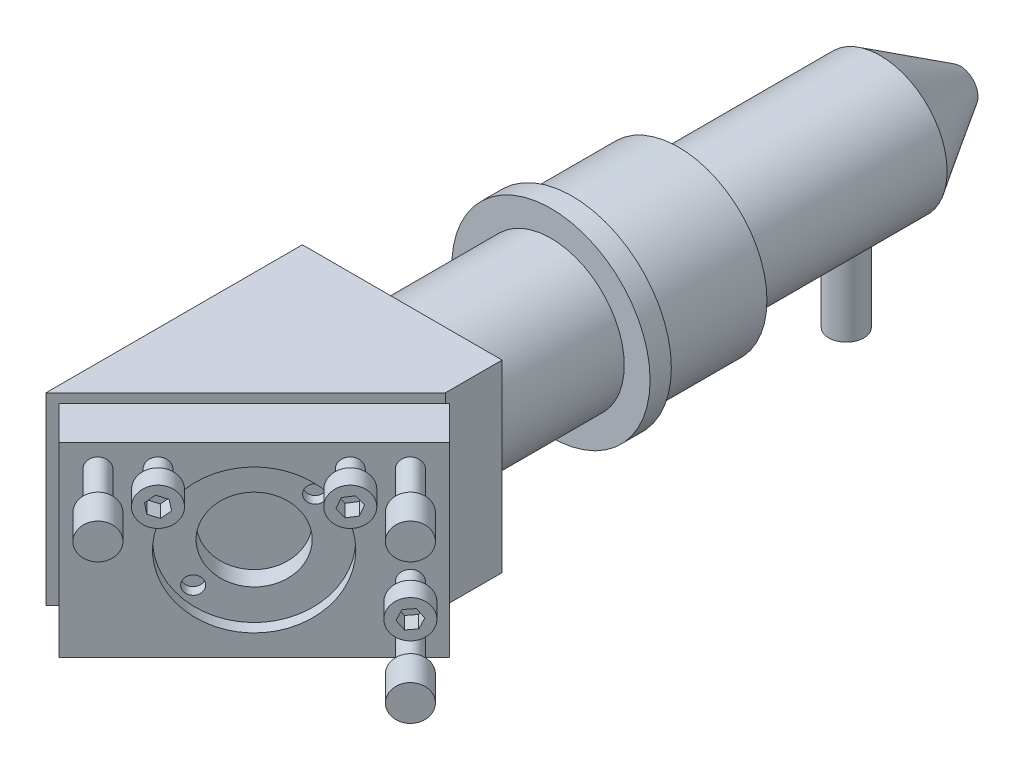
SolidWorks part; units mm, degrees
ref_plane "Front" through (0, 0, 0) normal (0, 0, 1) x (1, 0, 0)
ref_plane "laser vertical plane" through (0, 0, 0) normal (0, 1, 0) x (1, 0, 0)
ref_plane "Right" through (0, 0, 0) normal (1, 0, 0) x (0, 0, -1)
sketch "Sketch1" plane through (0, 0, 0) normal (0, 0, 1) x (1, 0, 0)
  line L1 (-14.1, 13) -> (14.1, 13)
  line L2 (-14.1, 13) -> (-14.1, -13)
  line L3 (-14.1, -13) -> (14.1, -13)
  line L4 (14.1, 13) -> (14.1, -13)
  line L5 (-14.1, 13) -> (14.1, -13) construction
  line L6 (-14.1, -13) -> (14.1, 13) construction
  point P0 (0, 0)
  dimension "D1" = 26
  dimension "D2" = 28.2
extrude "Boss-Extrude1" add sketch "Sketch1" along normal blind 60
sketch "Sketch2" plane through (0, -13, 0) normal (0, -1, 0) x (1, 0, 0)
  line L0 (-14.1, 60) -> (-14.1, 0) construction
  line L1 (-14.1, 60) -> (14.1, 60) construction
  line L2 (14.1, 60) -> (14.1, 0) construction
  line L3 (-14.1, 60) -> (-14.1, 36.2)
  line L4 (-14.1, 60) -> (14.1, 60)
  line L5 (14.1, 60) -> (14.1, 8)
  line L6 (-14.1, 36.2) -> (14.1, 8)
  line L7 (-14.1, 0) -> (14.1, 0) construction
  dimension "D1" = 8
  dimension "D2" = 45
extrude "Cut-Extrude1" cut sketch "Sketch2" against normal through all
sketch "Sketch3" plane through (0, 0, 0) normal (0, 0, -1) x (-1, 0, 0)
  circle A0 centre (0, 0) radius 6
  dimension "D1" = 12
extrude "Cut-Extrude2" cut sketch "Sketch3" against normal blind 60
sketch "Sketch4" plane through (0, 0, 0) normal (0, 0, -1) x (-1, 0, 0)
  line L0 (0, 0) -> (0, -21.9325) construction
  line L1 (0, 0) -> (-18.8944, 0) construction
  circle A0 centre (9.75, -10) radius 1.5
  circle A1 centre (-9.75, -10) radius 1.5
  circle A2 centre (-9.75, 10) radius 1.5
  circle A3 centre (9.75, 10) radius 1.5
  dimension "D1" = 3
  dimension "D2" = 19.5
  dimension "D3" = 20
extrude "Cut-Extrude3" cut sketch "Sketch4" against normal blind 6
sketch "Sketch5" plane through (-14.1, 0, 0) normal (-1, 0, 0) x (0, 0, 1)
  line L0 (0, 0) -> (32.3952, 0) construction
  line L1 (0, 13) -> (0, -13) construction
  circle A0 centre (21.5, 0) radius 8.5
  dimension "D1" = 17
  dimension "D2" = 13
extrude "Cut-Extrude4" cut sketch "Sketch5" against normal through all
sketch "Sketch6" plane through (11.05, 0, 11.05) normal (0.7071, 0, 0.7071) x (0.7071, 0, -0.7071)
  line L0 (0, 0) -> (38.833, 0) construction
  line L1 (4.3134, 13) -> (4.3134, -13) construction
  circle A0 centre (-14.7866, 0) radius 11.7
  point P5 (-10.2089, 2.6303)
  dimension "D1" = 23.4
  dimension "D2" = 7.4
extrude "Cut-Extrude5" cut sketch "Sketch6" against normal blind 2.2
ref_plane "laser Z plane" through (0, 0, 21.5) normal (0, 0, -1) x (-1, 0, 0)
sketch "Sketch7" plane through (11.05, 0, 11.05) normal (0.7071, 0, 0.7071) x (0.7071, 0, -0.7071)
  line L0 (0, 0) -> (-50.829, 0) construction
  line L1 (-14.7866, 0) -> (-14.7866, 27.5836) construction
  circle A0 centre (-30.3866, 9.875) radius 1.5
  circle A1 centre (0.8134, 9.875) radius 1.5
  circle A2 centre (0.8134, -9.875) radius 1.5
  point P10 (0, 0)
  point P11 (0, 0)
  dimension "D1" = 3
  dimension "D2" = 31.2
  dimension "D3" = 19.75
extrude "Boss-Extrude2" add sketch "Sketch7" along normal blind 21.3
sketch "Sketch8" plane through (26.1114, 0, 26.1114) normal (0.7071, 0, 0.7071) x (0.7071, 0, -0.7071)
  circle A0 centre (-30.3866, 9.875) radius 2.5
  circle A1 centre (-30.3866, 9.875) radius 1.5 construction
  circle A2 centre (0.8134, 9.875) radius 2.5
  circle A3 centre (0.8134, -9.875) radius 2.5
  dimension "D1" = 5
extrude "Boss-Extrude3" add sketch "Sketch8" against normal blind 5
ref_plane "Plane2" through (12.4642, 0, 12.4642) normal (0.7071, 0, 0.7071) x (0.7071, 0, -0.7071)
sketch "Sketch9" plane through (12.4642, 0, 12.4642) normal (0.7071, 0, 0.7071) x (0.7071, 0, -0.7071)
  line L0 (0, 0) -> (-55.05, 0) construction
  line L1 (-14.7866, 0) -> (-14.7866, 25.2669) construction
  line L3 (4.7134, 13.125) -> (-34.2866, 13.125)
  line L4 (4.7134, 13.125) -> (4.7134, -13.125)
  line L5 (4.7134, -13.125) -> (-34.2866, -13.125)
  line L6 (-34.2866, 13.125) -> (-34.2866, -13.125)
  line L7 (4.7134, 13.125) -> (-34.2866, -13.125) construction
  line L8 (4.7134, -13.125) -> (-34.2866, 13.125) construction
  arc A0 (-3.4246, 2.7918) -> (-26.1649, 2.7249) centre (-14.7866, 0) ccw construction
  arc A1 (-3.4246, 2.7918) -> (-26.1649, 2.7249) centre (-14.7866, 0) ccw construction
  circle A2 centre (-14.7866, 0) radius 10.15
  dimension "D3" = 20.3
  dimension "D1" = 26.25
  dimension "D2" = 39
extrude "Boss-Extrude4" add sketch "Sketch9" along normal blind 6.8
sketch "Sketch10" plane through (0, 0, 0) normal (0, 1, 0) x (1, 0, 0)
  line L0 (5.1206, -26.0321) -> (18.2949, -39.2064) construction
  line L1 (6.8168, -27.7283) -> (2.0085, -22.92) construction
  line L2 (9.1856, -15.7428) -> (-5.1687, -30.0971) construction
  line L3 (9.1856, -15.7428) -> (-5.1687, -30.0971) construction
  line L4 (-5.1687, -30.0971) -> (-5.7697, -30.6981)
  line L5 (-5.7697, -30.6981) -> (-5.7697, -29.2839)
  line L6 (-5.7697, -29.2839) -> (-5.1545, -28.6687)
  line L7 (-5.1545, -28.6687) -> (-4.4474, -28.6687)
  line L8 (-4.4474, -28.6687) -> (-4.0939, -29.0223)
  line L9 (-4.0939, -29.0223) -> (-5.1687, -30.0971)
  point P12 (0, 0)
  dimension "D1" = 45
  dimension "D2" = 45
  dimension "D3" = 1
  dimension "D4" = 22
  dimension "D5" = 17.26
  dimension "D6" = 0.5
revolve "Revolve1" add sketch "Sketch10" angle 360 about L0
sketch "Sketch11" plane through (12.4642, 0, 12.4642) normal (0.7071, 0, 0.7071) x (0.7071, 0, -0.7071)
  circle A0 centre (-14.7866, 0) radius 10
  dimension "D1" = 20
extrude "Boss-Extrude5" add sketch "Sketch11" along normal blind 2
sketch "Sketch12" plane through (13.8784, 0, 13.8784) normal (0.7071, 0, 0.7071) x (0.7071, 0, -0.7071)
  circle A0 centre (-14.7866, 0) radius 5.8
  circle A1 centre (-14.7866, 0) radius 10.15 construction
  circle A2 centre (-14.7866, 0) radius 10.15
  dimension "D1" = 11.6
extrude "Boss-Extrude6" add sketch "Sketch12" along normal blind 3
sketch "Sketch20" plane through (15.9997, 0, 15.9997) normal (0.7071, 0, 0.7071) x (0.7071, 0, -0.7071)
  line L0 (-14.7866, 0) -> (-20.8738, -5.5686) construction
  line L1 (-14.7866, 0) -> (-9.2181, -6.0871) construction
  circle A0 centre (-14.7866, 0) radius 8.25 construction
  circle A1 centre (-20.8738, -5.5686) radius 1.25
  circle A2 centre (-8.6995, 5.5686) radius 1.25
  dimension "D1" = 16.5
  dimension "D2" = 2.5
extrude "Cut-Extrude7" cut sketch "Sketch20" against normal blind 1.5
sketch "Sketch13" plane through (17.2725, 0, 17.2725) normal (0.7071, 0, 0.7071) x (0.7071, 0, -0.7071)
  line L0 (0.8134, -9.875) -> (0.8134, 9.875) construction
  line L1 (0.8134, 9.875) -> (-30.3866, 9.875) construction
  circle A0 centre (-24.3866, 9.875) radius 1.5
  circle A1 centre (-5.1866, 9.875) radius 1.5
  circle A2 centre (0.8134, -3.875) radius 1.5
  point P12 (0, 0)
  point P13 (0, 0)
  dimension "D1" = 3
  dimension "D2" = 6
  dimension "D3" = 6
  dimension "D4" = 6
extrude "Boss-Extrude7" add sketch "Sketch13" along normal blind 3.5 and the other way up to surface (11 mm away)
sketch "Sketch14" plane through (19.7474, 0, 19.7474) normal (0.7071, 0, 0.7071) x (0.7071, 0, -0.7071)
  circle A0 centre (0.8134, -3.875) radius 2.65
  circle A1 centre (-5.1866, 9.875) radius 2.65
  circle A2 centre (-24.3866, 9.875) radius 2.65
  dimension "D1" = 5.3
extrude "Boss-Extrude8" add sketch "Sketch14" along normal blind 0.5
sketch "Sketch15" plane through (20.101, 0, 20.101) normal (0.7071, 0, 0.7071) x (0.7071, 0, -0.7071)
  line L1 (-23.2738, 10.7941) -> (-24.6262, 11.2984)
  line L2 (-24.6262, 11.2984) -> (-25.7391, 10.3792)
  line L3 (-25.7391, 10.3792) -> (-25.4995, 8.9559)
  line L4 (-25.4995, 8.9559) -> (-24.1471, 8.4516)
  line L5 (-24.1471, 8.4516) -> (-23.0342, 9.3708)
  line L6 (-23.0342, 9.3708) -> (-23.2738, 10.7941)
  line L7 (-3.7605, 10.0975) -> (-4.6662, 11.2213)
  line L8 (-4.6662, 11.2213) -> (-6.0924, 10.9988)
  line L9 (-6.0924, 10.9988) -> (-6.6128, 9.6525)
  line L10 (-6.6128, 9.6525) -> (-5.7071, 8.5287)
  line L11 (-5.7071, 8.5287) -> (-4.2809, 8.7512)
  line L12 (-4.2809, 8.7512) -> (-3.7605, 10.0975)
  line L13 (1.6464, -5.0537) -> (2.2507, -3.7429)
  line L14 (2.2507, -3.7429) -> (1.4176, -2.5642)
  line L15 (1.4176, -2.5642) -> (-0.0197, -2.6963)
  line L16 (-0.0197, -2.6963) -> (-0.624, -4.0071)
  line L17 (-0.624, -4.0071) -> (0.2091, -5.1858)
  line L18 (0.2091, -5.1858) -> (1.6464, -5.0537)
  circle A0 centre (0.8134, -3.875) radius 2.65 construction
  circle A1 centre (-5.1866, 9.875) radius 2.65 construction
  circle A2 centre (-24.3866, 9.875) radius 2.65 construction
  circle A3 centre (0.8134, -3.875) radius 2.65
  circle A4 centre (-5.1866, 9.875) radius 2.65
  circle A5 centre (-24.3866, 9.875) radius 2.65
  circle A6 centre (-24.3866, 9.875) radius 1.25 construction
  circle A7 centre (-5.1866, 9.875) radius 1.25 construction
  circle A8 centre (0.8134, -3.875) radius 1.25 construction
  dimension "D1" = 2.5
extrude "Boss-Extrude9" add sketch "Sketch15" along normal blind 2.5
sketch "Sketch16" plane through (0, 0, 0) normal (0, 1, 0) x (1, 0, 0)
  line L0 (0, 0) -> (0, 86.4441) construction
  line L1 (0, 0) -> (56.7966, 0) construction
  line L2 (8, 0) -> (10.35, 0)
  line L3 (10.35, 0) -> (10.35, 21)
  line L4 (10.35, 21) -> (14, 21)
  line L5 (14, 21) -> (14, 24)
  line L6 (14, 24) -> (12.5, 24)
  line L7 (12.5, 24) -> (12.5, 39)
  line L8 (12.5, 39) -> (9.44, 39)
  line L9 (9.44, 39) -> (9.44, 67.5)
  line L10 (9.44, 67.5) -> (2.5, 78.8)
  line L11 (2.5, 78.8) -> (2.1, 78.8)
  line L12 (2.1, 78.8) -> (6.65, 67.5)
  line L13 (6.65, 67.5) -> (6.65, 37)
  line L14 (6.65, 37) -> (9, 37)
  line L15 (9, 37) -> (9, 30.4)
  line L16 (9, 30.4) -> (8, 30.4)
  line L17 (8, 30.4) -> (8, 0)
  line L18 (14.1, 0) -> (-14.1, 0) construction
  point P3 (0, 0)
  dimension "D1" = 18
  dimension "D2" = 16
  dimension "D3" = 20.7
  dimension "D4" = 28
  dimension "D5" = 3
  dimension "D6" = 21
  dimension "D7" = 25
  dimension "D8" = 13.3
  dimension "D9" = 18.88
  dimension "D10" = 4.2
  dimension "D11" = 5
  dimension "D12" = 28.5
  dimension "D13" = 39.8
  dimension "D14" = 13
  dimension "D15" = 15
  dimension "D16" = 6.4
revolve "Revolve2" add sketch "Sketch16" angle 360 about L0
sketch "Sketch17" plane through (0, 0, -37) normal (0, 0, 1) x (1, 0, 0)
  circle A0 centre (0, 0) radius 9
  dimension "D1" = 18
extrude "lens" add sketch "Sketch17" along normal blind 2
ref_plane "focal lens midplane" through (0, 0, -36) normal (0, 0, 1) x (1, 0, 0)
ref_plane "cutting plane" through (0, 0, -86.8) normal (0, 0, -1) x (-1, 0, 0)
sketch "Sketch18" plane through (0, 0, -35) normal (0, 0, 1) x (1, 0, 0)
  circle A0 centre (0, 0) radius 5.9
  circle A1 centre (0, 0) radius 9
  circle A2 centre (0, 0) radius 9
  dimension "D2" = 11.8
  dimension "D1" = 0
extrude "Boss-Extrude11" add sketch "Sketch18" along normal blind 3
chamfer "Chamfer1" distance 1 angle 45 1 edges at (5.9, 0, -32)
sketch "Sketch19" plane through (0, 0, -32) normal (0, 0, 1) x (1, 0, 0)
  line L0 (0, 0) -> (-5.5335, 5.0626) construction
  line L1 (0, 0) -> (13.8088, 15.0931) construction
  circle A0 centre (0, 0) radius 7.5 construction
  circle A1 centre (-5.5335, 5.0626) radius 1
  circle A2 centre (5.5335, -5.0626) radius 1
  dimension "D1" = 15
  dimension "D2" = 2
extrude "Cut-Extrude6" cut sketch "Sketch19" against normal blind 1.5
ref_plane "Plane5" through (0, -9.44, 0) normal (0, -1, 0) x (-1, 0, 0)
sketch "Sketch21" plane through (0, -9.44, 0) normal (0, -1, 0) x (-1, 0, 0)
  line L0 (0, 0) -> (0, 51.5042) construction
  line L1 (2.5, 78.8) -> (-2.5, 78.8) construction
  circle A0 centre (0, 62.7) radius 2.5
  point P5 (0, 0)
  dimension "D1" = 5
  dimension "D2" = 13.6
extrude "Boss-Extrude12" add sketch "Sketch21" along normal blind 12 and the other way up to surface separate body
sketch "Sketch22" plane through (0, -21.44, 0) normal (0, -1, 0) x (1, 0, 0)
  circle A0 centre (0, -62.7) radius 1.25
  dimension "D1" = 2.5
extrude "Cut-Extrude8" cut sketch "Sketch22" against normal blind 17
